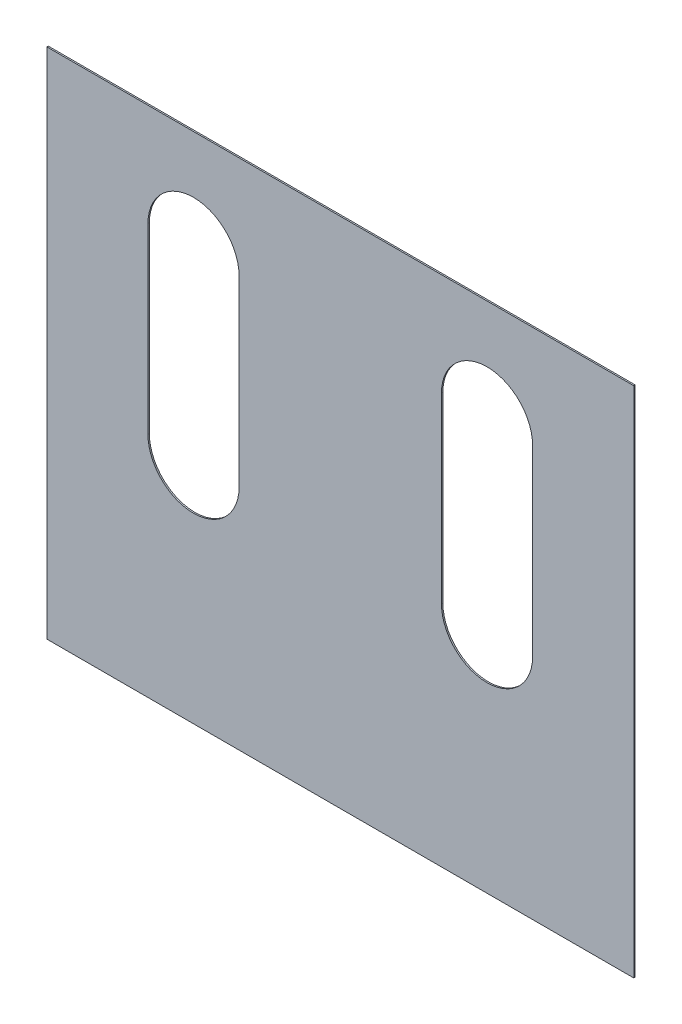
SolidWorks part; units mm, degrees
material "S-Glass Fiber"
ref_plane "Front Plane" through (0, 0, 0) normal (0, 0, 1) x (1, 0, 0)
ref_plane "Top Plane" through (0, 0, 0) normal (0, 1, 0) x (1, 0, 0)
ref_plane "Right Plane" through (0, 0, 0) normal (1, 0, 0) x (0, 0, -1)
sketch "Sketch1" plane through (0, 0, 0) normal (0, 0, 1) x (1, 0, 0)
  line L0 (-654.05, 685.8) -> (-654.05, -127) construction
  line L1 (-1308.1, -1143) -> (1308.1, -1143)
  line L2 (-1308.1, -1143) -> (-1308.1, 1143)
  line L3 (-1308.1, 1143) -> (1308.1, 1143)
  line L4 (1308.1, -1143) -> (1308.1, 1143)
  line L5 (-1308.1, -1143) -> (1308.1, 1143) construction
  line L6 (-1308.1, 1143) -> (1308.1, -1143) construction
  line L11 (-450.85, 685.8) -> (-450.85, -127)
  line L12 (-857.25, 685.8) -> (-857.25, -127)
  line L13 (654.05, 685.8) -> (654.05, -127) construction
  line L14 (857.25, 685.8) -> (857.25, -127)
  line L15 (450.85, 685.8) -> (450.85, -127)
  arc A0 (-450.85, 685.8) -> (-857.25, 685.8) centre (-654.05, 685.8) ccw
  arc A1 (-857.25, -127) -> (-450.85, -127) centre (-654.05, -127) ccw
  arc A2 (857.25, 685.8) -> (450.85, 685.8) centre (654.05, 685.8) ccw
  arc A3 (450.85, -127) -> (857.25, -127) centre (654.05, -127) ccw
  point P0 (0, 0)
  point P6 (0, 0)
  point P9 (-654.05, 279.4)
  point P14 (654.05, 279.4)
  dimension "D7" = 812.8
  dimension "D9" = 457.2
  dimension "D10" = 457.2
  dimension "D1" = 2286
  dimension "D2" = 2616.2
  dimension "D3" = 406.4
  dimension "D4" = 406.4
  dimension "D5" = 450.85
  dimension "D6" = 450.85
  dimension "D8" = 812.8
extrude "Boss-Extrude1" add sketch "Sketch1" along normal blind 6.35
